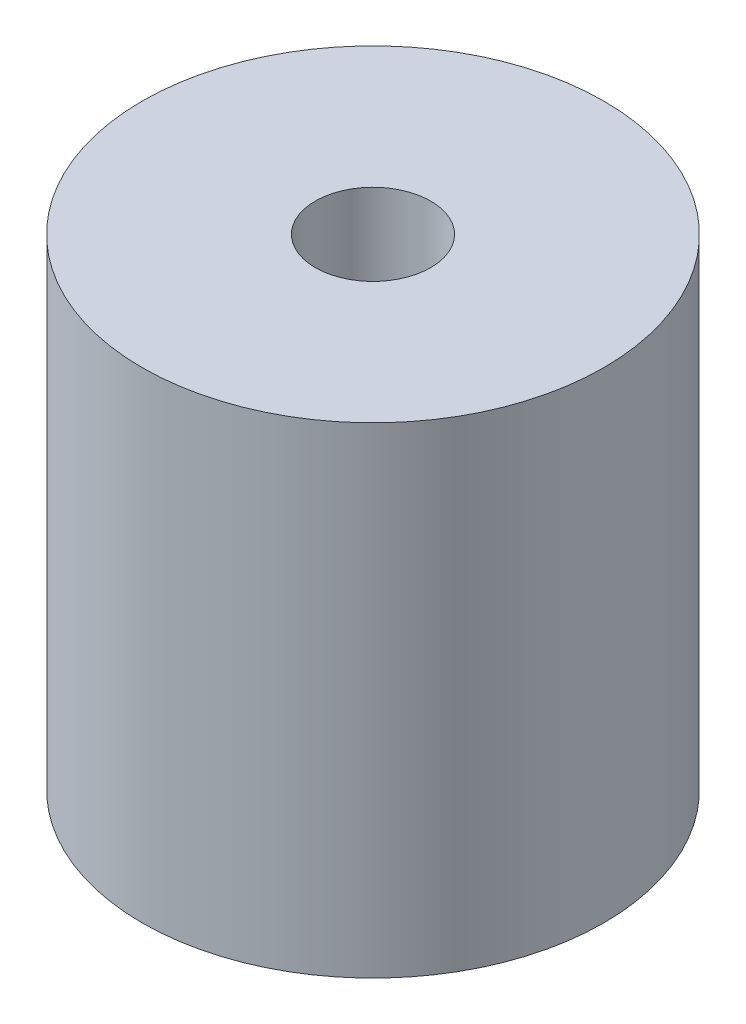
SolidWorks part; units mm, degrees
ref_plane "Front Plane" through (0, 0, 0) normal (0, 0, 1) x (1, 0, 0)
ref_plane "Top Plane" through (0, 0, 0) normal (0, 1, 0) x (1, 0, 0)
ref_plane "Right Plane" through (0, 0, 0) normal (1, 0, 0) x (0, 0, -1)
sketch "Sketch1" plane through (0, 0, 0) normal (0, 1, 0) x (1, 0, 0)
  circle A0 centre (0, 0) radius 24
  circle A1 centre (0, 0) radius 6
  dimension "D1" = 48
  dimension "D2" = 12
extrude "Boss-Extrude1" add sketch "Sketch1" along normal blind 50
